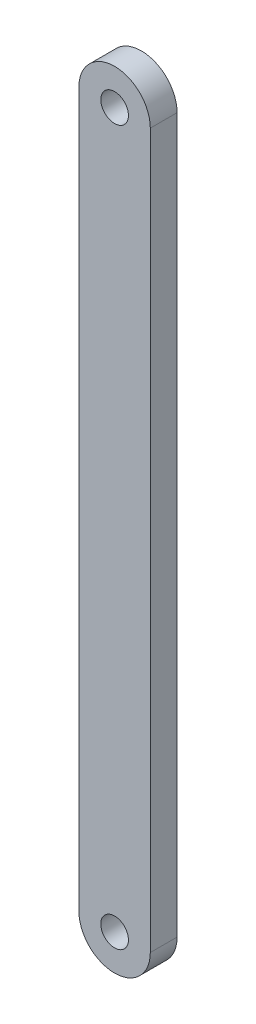
SolidWorks part; units mm, degrees
ref_plane "Front Plane" through (0, 0, 0) normal (0, 0, 1) x (1, 0, 0)
ref_plane "Top Plane" through (0, 0, 0) normal (0, 1, 0) x (1, 0, 0)
ref_plane "Right Plane" through (0, 0, 0) normal (1, 0, 0) x (0, 0, -1)
sketch "Model" plane through (0, 0, 0) normal (0, 0, 1) x (1, 0, 0)
  line L0 (56, 80) -> (56, 0)
  line L1 (64, 80) -> (64, 0)
  circle A0 centre (60, 80) radius 1.55
  circle A1 centre (60, 0) radius 1.55
  arc A2 (64, 80) -> (56, 80) centre (60, 80) ccw
  arc A3 (56, 0) -> (64, 0) centre (60, 0) ccw
extrude "Boss-Extrude1" add sketch "Model" along normal blind 3
